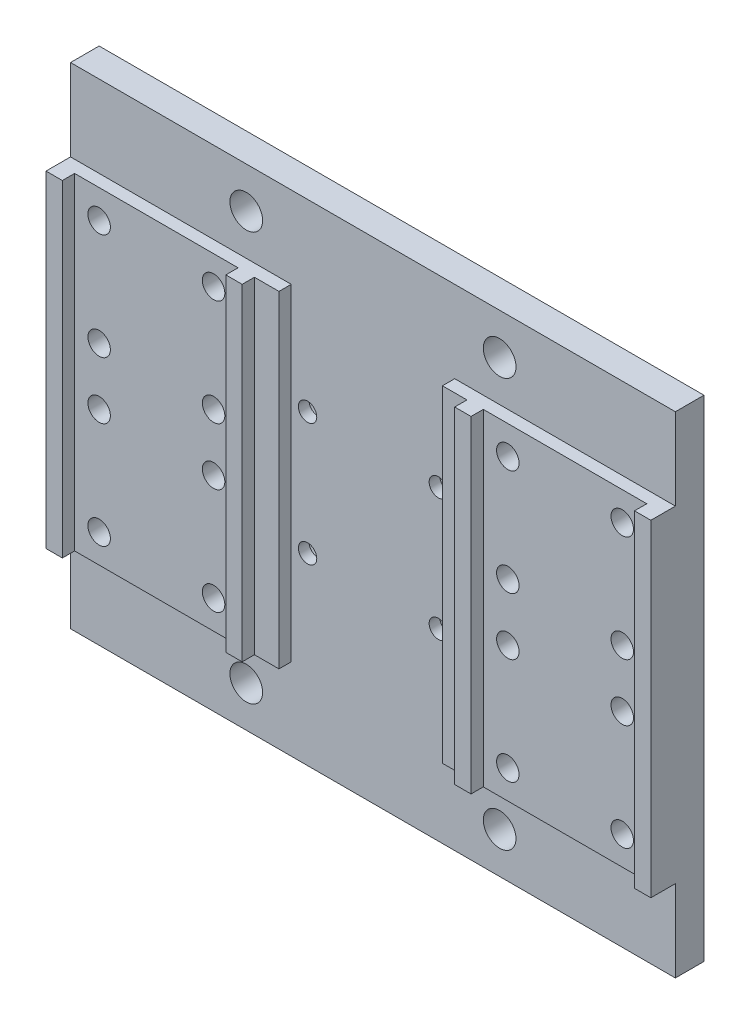
SolidWorks part; units mm, degrees
ref_plane "Plan de face" through (0, 0, 0) normal (0, 0, 1) x (1, 0, 0)
ref_plane "Plan de dessus" through (0, 0, 0) normal (0, 1, 0) x (1, 0, 0)
ref_plane "Plan de droite" through (0, 0, 0) normal (1, 0, 0) x (0, 0, -1)
sketch "Esquisse1" plane through (0, 0, 0) normal (0, 0, 1) x (1, 0, 0)
  line L0 (0, 80.3793) -> (0, -91.4076) construction
  line L1 (-74, 66.3924) -> (74, 66.3924)
  line L2 (-74, 66.3924) -> (-74, -53.6076)
  line L3 (-74, -53.6076) -> (74, -53.6076)
  line L4 (74, 66.3924) -> (74, -53.6076)
  line L5 (74, -0.6076) -> (-74, -0.6076) construction
  line L6 (74, -26.6076) -> (-74, -26.6076) construction
  line L7 (20, 66.3924) -> (20, -53.6076) construction
  line L8 (-20, 66.3924) -> (-20, -53.6076) construction
  line L9 (30, 66.3924) -> (30, -53.6076) construction
  line L10 (-30, 66.3924) -> (-30, -53.6076) construction
  line L11 (-64, -0.6076) -> (-64, -26.6076) construction
  line L12 (-36, -0.6076) -> (-36, -26.6076) construction
  line L13 (36, -0.6076) -> (36, -26.6076) construction
  line L14 (64, -0.6076) -> (64, -26.6076) construction
  line L15 (-50, 66.3924) -> (-50, -53.6076) construction
  line L16 (50, 66.3924) -> (50, -53.6076) construction
  line L17 (64, 60.7865) -> (64, 9.7193) construction
  line L18 (64, 9.7193) -> (63.9829, 22.6659) construction
  line L19 (36, 63.8822) -> (36, 12.815) construction
  line L20 (69.737, 39.3924) -> (-93.774, 39.3924) construction
  line L21 (16, -53.6076) -> (16, 66.3924) construction
  line L22 (-16, -53.6076) -> (-16, 66.3924) construction
  line L23 (69.737, 13.3924) -> (-93.774, 13.3924) construction
  line L24 (-64, 60.7865) -> (-64, 26.2622) construction
  line L25 (-36, 60.7865) -> (-36, 26.2622) construction
  circle A0 centre (-64, -0.6076) radius 2.5
  circle A1 centre (-36, -0.6076) radius 2.5
  circle A2 centre (-64, -26.6076) radius 2.5
  circle A3 centre (-36, -26.6076) radius 2.5
  circle A4 centre (36, -0.6076) radius 2.5
  circle A5 centre (64, -0.6076) radius 2.5
  circle A6 centre (36, -26.6076) radius 2.5
  circle A7 centre (64, -26.6076) radius 2.5
  circle A8 centre (64, 39.3924) radius 2.5
  circle A9 centre (36, 39.3924) radius 2.5
  circle A10 centre (16, 21.3924) radius 2
  circle A11 centre (16, -8.6076) radius 2
  circle A12 centre (-16, 21.3924) radius 2
  circle A13 centre (-16, -8.6076) radius 2
  circle A14 centre (64, 13.3924) radius 2.5
  circle A15 centre (36, 13.3924) radius 2.5
  circle A16 centre (-36, 39.3924) radius 2.5
  circle A17 centre (-64, 39.3924) radius 2.5
  circle A18 centre (-36, 13.3924) radius 2.5
  circle A19 centre (-64, 13.3924) radius 2.5
  dimension "D9" = 5
  dimension "D10" = 5
  dimension "D11" = 5
  dimension "D12" = 5
  dimension "D13" = 5
  dimension "D14" = 5
  dimension "D15" = 5
  dimension "D16" = 5
  dimension "D26" = 20
  dimension "D27" = 20
  dimension "D31" = 5
  dimension "D32" = 5
  dimension "D30" = 5
  dimension "D33" = 4
  dimension "D34" = 4
  dimension "D41" = 4
  dimension "D42" = 4
  dimension "D44" = 45
  dimension "D46" = 45
  dimension "D36" = 5
  dimension "D37" = 5
  dimension "D38" = 5
  dimension "D39" = 5
  dimension "D47" = 5
  dimension "D1" = 148
  dimension "D2" = 120
  dimension "D5" = 16
  dimension "D6" = 16
  dimension "D7" = 40
  dimension "D8" = 20
  dimension "D17" = 26
  dimension "D18" = 28
  dimension "D19" = 10
  dimension "D20" = 27
  dimension "D21" = 28
  dimension "D22" = 26
  dimension "D23" = 10
  dimension "D24" = 14
  dimension "D25" = 14
  dimension "D28" = 27
  dimension "D29" = 26
  dimension "D35" = 27
  dimension "D40" = 74
  dimension "D43" = 45
  dimension "D45" = 45
extrude "Extrusion1" add sketch "Esquisse1" along normal blind 4
sketch "Esquisse4" plane through (0, 0, 4) normal (0, 0, 1) x (1, 0, 0)
  line L0 (-74, 66.3924) -> (-74, -53.6076) construction
  line L1 (-74, 46.3924) -> (-20, 46.3924)
  line L2 (-74, 46.3924) -> (-74, -33.6076)
  line L3 (-74, -33.6076) -> (-20, -33.6076)
  line L4 (-20, 46.3924) -> (-20, -33.6076)
  line L5 (74, -53.6076) -> (74, 66.3924) construction
  line L6 (74, 46.3924) -> (20, 46.3924)
  line L7 (74, 46.3924) -> (74, -33.6076)
  line L8 (74, -33.6076) -> (20, -33.6076)
  line L9 (20, 46.3924) -> (20, -33.6076)
  line L10 (0, 66.3924) -> (0, -53.6076) construction
  line L11 (74, 66.3924) -> (-74, 66.3924) construction
  line L12 (-74, -53.6076) -> (74, -53.6076) construction
  line L13 (-74, 6.3924) -> (74, 6.3924) construction
  dimension "D1" = 40
  dimension "D2" = 20
  dimension "D3" = 80
  dimension "D4" = 80
  dimension "D5" = 40
  dimension "D6" = 40
extrude "Boss.-Extru.1" add sketch "Esquisse4" along normal blind 3
sketch "Esquisse6" plane through (0, 0, 0) normal (0, 0, -1) x (-1, 0, 0)
  line L1 (-74, 66.3924) -> (74, 66.3924)
  line L2 (-74, 66.3924) -> (-74, -53.6076)
  line L3 (-74, -53.6076) -> (74, -53.6076)
  line L4 (74, 66.3924) -> (74, -53.6076)
extrude "Boss.-Extru.2" add sketch "Esquisse6" along normal blind 3
hole_wizard "Chambrage pour vis à tête hexagonale M41" positions "Esquisse8" profile "Esquisse7" counterbore size "M4" standard "ISO" end condition through all
sketch "Esquisse8" plane through (0, 0, -3) normal (0, 0, -1) x (-1, 0, 0)
  line L0 (-74, -53.6076) -> (74, -53.6076) construction
  line L1 (74, 66.3924) -> (-74, 66.3924) construction
  line L2 (0, 66.3924) -> (0, -53.6076) construction
  point P0 (-16, 21.3924)
  point P2 (16, 21.3924)
  point P4 (16, -8.6076)
  point P6 (-16, -8.6076)
  dimension "D1" = 45
  dimension "D2" = 45
  dimension "D3" = 45
  dimension "D4" = 45
  dimension "D5" = 16
  dimension "D6" = 16
  dimension "D7" = 16
  dimension "D8" = 16
sketch "Esquisse7" plane through (16, 21.3924, -3) normal (1, 0, 0) x (0, 1, 0)
  line L0 (0, 0) -> (0, 10)
  line L1 (0, 10) -> (2.25, 10)
  line L3 (2.25, 10) -> (2.25, 4.4)
  line L4 (2.25, 4.4) -> (5, 4.4)
  line L5 (5, 4.4) -> (5, 0)
  line L7 (5, 0) -> (0, 0)
  line L11 (0, -6.35) -> (0, 107.95) construction
  dimension "Diamètre du perçage jusqu'au prochain" = 4.5
  dimension "Profondeur du perçage jusqu'au prochain" = 10
  dimension "Diamètre du chambrage" = 10
  dimension "Profondeur du chambrage" = 4.4
hole_wizard "Chambrage pour vis à tête hexagonale M51" positions "Esquisse10" profile "Esquisse9" counterbore size "M5" standard "ISO" end condition through all
sketch "Esquisse10" plane through (0, 0, -3) normal (0, 0, -1) x (-1, 0, 0)
  line L0 (-30, 66.3924) -> (-30, -53.6076) construction
  line L1 (74, 66.3924) -> (-74, 66.3924) construction
  line L2 (-74, -53.6076) -> (74, -53.6076) construction
  line L5 (30, 66.3924) -> (30, -53.6076) construction
  line L8 (0, 66.3924) -> (0, -53.6076) construction
  line L11 (-74, 6.3924) -> (74, 6.3924) construction
  line L12 (-74, 66.3924) -> (-74, -53.6076) construction
  line L13 (74, -53.6076) -> (74, 66.3924) construction
  point P0 (-64, -0.6076)
  point P2 (-36, -0.6076)
  point P4 (-36, -26.6076)
  point P6 (-64, -26.6076)
  point P8 (36, -0.6076)
  point P10 (64, -0.6076)
  point P12 (64, -26.6076)
  point P14 (36, -26.6076)
  point P53 (64, 39.3924)
  point P55 (64, 13.3924)
  point P57 (36, 39.3924)
  point P59 (36, 13.3924)
  point P61 (-36, 39.3924)
  point P63 (-64, 39.3924)
  point P65 (-64, 13.3924)
  point P67 (-36, 13.3924)
  dimension "D1" = 28
  dimension "D2" = 28
  dimension "D3" = 28
  dimension "D4" = 28
  dimension "D5" = 26
  dimension "D6" = 26
  dimension "D7" = 26
  dimension "D8" = 26
  dimension "D9" = 30
  dimension "D10" = 30
  dimension "D11" = 6
  dimension "D12" = 6
  dimension "D13" = 6
  dimension "D14" = 6
  dimension "D15" = 33
  dimension "D16" = 33
  dimension "D17" = 33
  dimension "D18" = 33
  dimension "D19" = 26
  dimension "D20" = 26
  dimension "D21" = 26
  dimension "D22" = 26
  dimension "D23" = 28
  dimension "D24" = 28
  dimension "D25" = 28
  dimension "D26" = 28
  dimension "D27" = 33
  dimension "D28" = 33
  dimension "D29" = 6
  dimension "D30" = 6
sketch "Esquisse9" plane through (64, -0.6076, -3) normal (1, 0, 0) x (0, 1, 0)
  line L0 (0, 0) -> (0, 10)
  line L1 (0, 10) -> (2.75, 10)
  line L3 (2.75, 10) -> (2.75, 5.4)
  line L4 (2.75, 5.4) -> (5.5, 5.4)
  line L5 (5.5, 5.4) -> (5.5, 0)
  line L7 (5.5, 0) -> (0, 0)
  line L11 (0, -6.35) -> (0, 107.95) construction
  dimension "Diamètre du perçage jusqu'au prochain" = 5.5
  dimension "Profondeur du perçage jusqu'au prochain" = 10
  dimension "Diamètre du chambrage" = 11
  dimension "Profondeur du chambrage" = 5.4
sketch "Esquisse11" plane through (0, 0, 7) normal (0, 0, 1) x (1, 0, 0)
  line L0 (-20, 46.3924) -> (-74, 46.3924) construction
  line L3 (-30, 46.3924) -> (-26, 46.3924)
  line L5 (-30, 46.3924) -> (-30, -33.6076)
  line L6 (-20, 46.3924) -> (-74, 46.3924) construction
  line L7 (-30, -33.6076) -> (-26, -33.6076)
  line L8 (74, 46.3924) -> (20, 46.3924) construction
  line L9 (26, 46.3924) -> (30, 46.3924)
  line L10 (26, 46.3924) -> (26, -33.6076)
  line L11 (26, -33.6076) -> (30, -33.6076)
  line L12 (30, 46.3924) -> (30, -33.6076)
  line L13 (20, -33.6076) -> (74, -33.6076) construction
  line L14 (-74, 66.3924) -> (74, 66.3924) construction
  line L15 (-70, 46.3924) -> (-74, 46.3924)
  line L16 (-70, 46.3924) -> (-70, -33.6076)
  line L17 (-70, -33.6076) -> (-74, -33.6076)
  line L18 (-74, 46.3924) -> (-74, -33.6076)
  line L19 (70, 46.3924) -> (74, 46.3924)
  line L20 (70, 46.3924) -> (70, -33.6076)
  line L21 (70, -33.6076) -> (74, -33.6076)
  line L22 (74, 46.3924) -> (74, -33.6076)
  line L23 (74, 66.3924) -> (-74, 66.3924) construction
  line L24 (-26, 46.3924) -> (-26, -33.6076)
  line L25 (-74, -33.6076) -> (-20, -33.6076) construction
  point P9 (0, 66.3924)
  point P34 (0, 66.3924)
  dimension "D1" = 4
  dimension "D2" = 4
  dimension "D3" = 4
  dimension "D4" = 4
  dimension "D5" = 30
  dimension "D6" = 30
extrude "Boss.-Extru.3" add sketch "Esquisse11" along normal blind 3
sketch "Esquisse3" plane through (0, 0, 4) normal (0, 0, 1) x (1, 0, 0)
  line L0 (74, 66.3924) -> (-74, 66.3924) construction
  line L2 (74, 66.3924) -> (74, -53.6076) construction
  line L3 (-74, -53.6076) -> (-74, 66.3924) construction
  circle A0 centre (-31, 56.3924) radius 4
  circle A1 centre (31, 56.3924) radius 4
  circle A2 centre (-31, -43.6076) radius 4
  circle A3 centre (31, -43.6076) radius 4
  dimension "D4" = 100
  dimension "D11" = 8
  dimension "D12" = 8
  dimension "D13" = 8
  dimension "D14" = 8
  dimension "D8" = 43
  dimension "D1" = 10
  dimension "D2" = 10
  dimension "D3" = 100
  dimension "D5" = 43
  dimension "D6" = 43
  dimension "D7" = 43
extrude "Enlèv. mat.-Extru.2" cut sketch "Esquisse3" against normal through all
